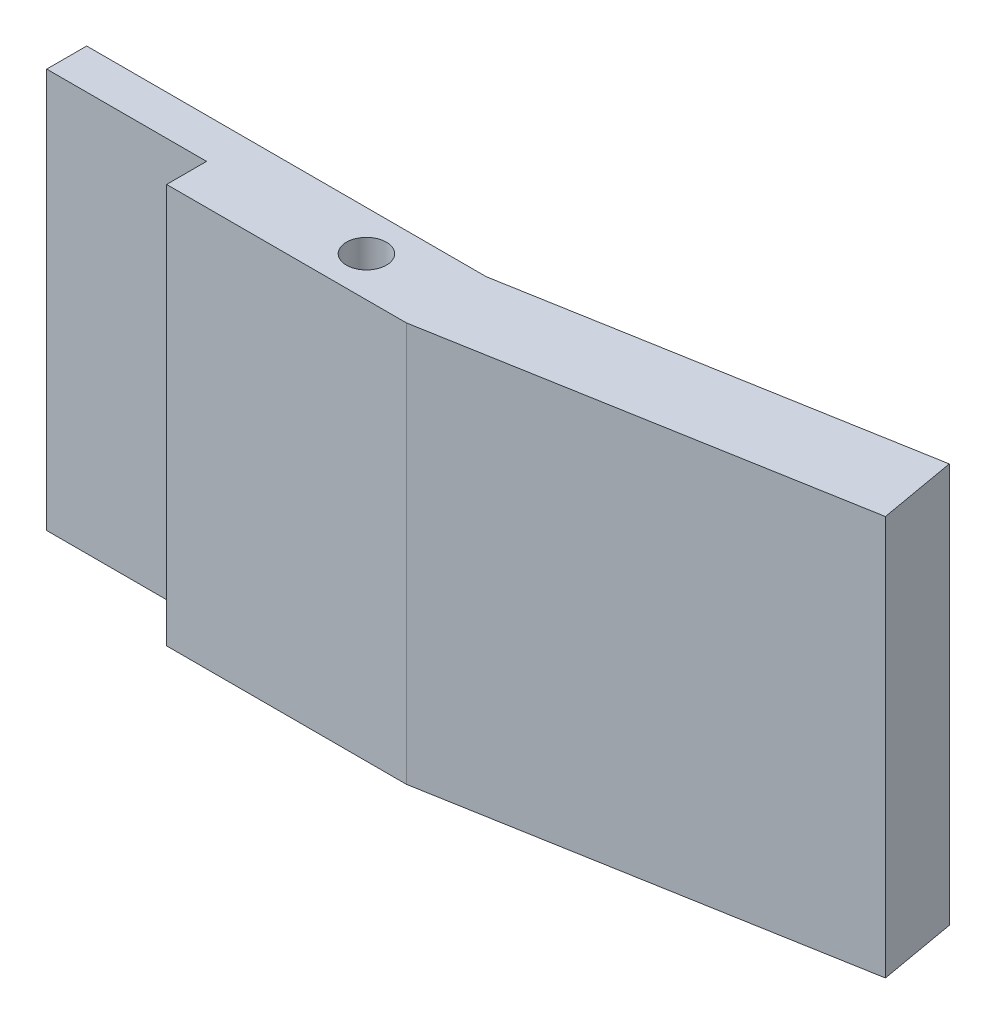
SolidWorks part; units mm, degrees
ref_plane "Front Plane" through (0, 0, 0) normal (0, 0, 1) x (1, 0, 0)
ref_plane "Top Plane" through (0, 0, 0) normal (0, 1, 0) x (1, 0, 0)
ref_plane "Right Plane" through (0, 0, 0) normal (1, 0, 0) x (0, 0, -1)
sketch "Sketch1" plane through (0, 0, 0) normal (0, 1, 0) x (1, 0, 0)
  line L4 (31.75, 0) -> (63.0176, 5.5133)
  line L5 (0, 0) -> (12.7, 0)
  line L6 (0, 0) -> (0, -3.175)
  line L7 (0, -3.175) -> (12.7, -3.175)
  line L8 (12.7, 0) -> (12.7, -3.175)
  line L9 (12.7, 0) -> (31.75, 0)
  line L10 (12.7, 0) -> (12.7, -6.35)
  line L11 (12.7, -6.35) -> (31.75, -6.35)
  line L12 (31.75, 0) -> (31.75, -6.35)
  line L13 (63.0176, 5.5133) -> (64.1036, -0.6452)
  line L14 (64.1036, -0.6452) -> (31.75, -6.35)
  line L15 (31.75, -6.35) -> (64.2, -6.35) construction
  circle A0 centre (25.4, -3.175) radius 1.5875
  point P2 (0, 0)
  dimension "D8" = 3.175
  dimension "D1" = 3.175
  dimension "D2" = 12.7
  dimension "D3" = 6.35
  dimension "D4" = 19.05
  dimension "D5" = 10
  dimension "D6" = 31.75
  dimension "D7" = 25.4
extrude "Boss-Extrude1" add sketch "Sketch1" along normal blind 31.75 contours L14 L13 L4 L12 | L12 L9 L8 L10 L11
